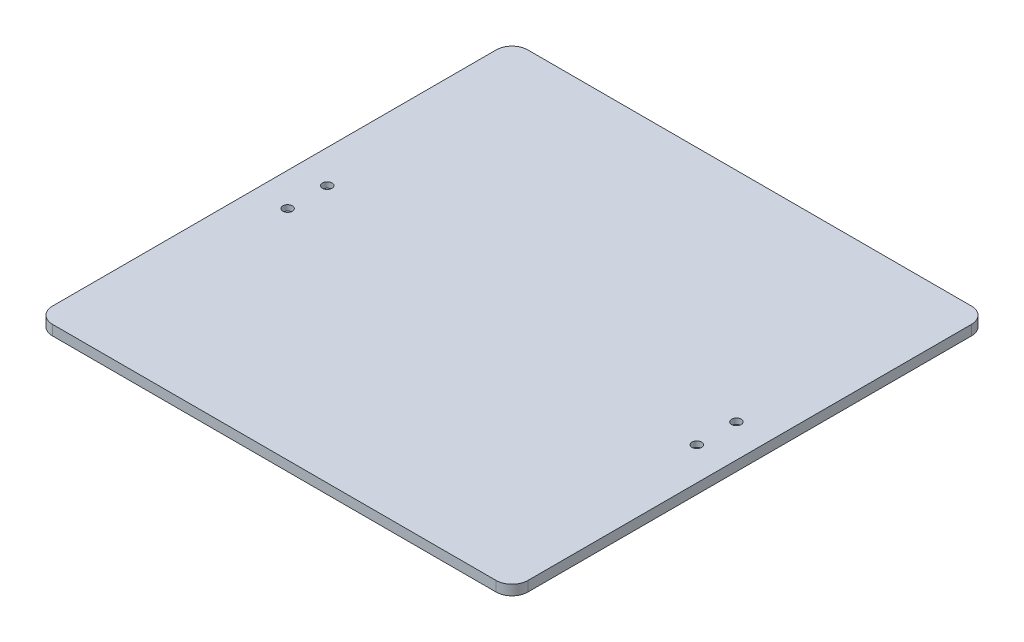
SolidWorks part; units mm, degrees
ref_plane "Front Plane" through (0, 0, 0) normal (0, 0, 1) x (1, 0, 0)
ref_plane "Top Plane" through (0, 0, 0) normal (0, 1, 0) x (1, 0, 0)
ref_plane "Right Plane" through (0, 0, 0) normal (1, 0, 0) x (0, 0, -1)
sketch "Sketch1" plane through (0, 0, 0) normal (0, 1, 0) x (1, 0, 0)
  line L1 (-150, 150) -> (150, 150)
  line L2 (-150, 150) -> (-150, -150)
  line L3 (-150, -150) -> (150, -150)
  line L4 (150, 150) -> (150, -150)
  line L5 (-150, 150) -> (150, -150) construction
  line L6 (-150, -150) -> (150, 150) construction
  point P0 (0, 0)
  dimension "D1" = 300
  dimension "D2" = 300
extrude "Boss-Extrude1" add sketch "Sketch1" along normal blind 6.35
fillet "Fillet1" radius 10 4 edges at (150, 3.175, -150) (150, 3.175, 150) (-150, 3.175, 150) (-150, 3.175, -150)
sketch "Sketch2" plane through (0, 6.35, 0) normal (0, 1, 0) x (1, 0, 0)
  line L0 (-150, 140) -> (-150, -140) construction
  line L1 (150, -140) -> (150, 140) construction
  line L2 (140, 150) -> (-140, 150) construction
  circle A0 centre (-129.12, 12.5) radius 1.75
  circle A1 centre (-129.12, -12.5) radius 1.75
  circle A2 centre (129.12, 12.5) radius 1.75
  circle A3 centre (129.12, -12.5) radius 1.75
  dimension "D1" = 3.5
  dimension "D2" = 3.5
  dimension "D3" = 3.5
  dimension "D4" = 3.5
  dimension "D5" = 20.88
  dimension "D6" = 20.88
  dimension "D7" = 20.88
  dimension "D8" = 20.88
  dimension "D9" = 137.5
  dimension "D10" = 137.5
  dimension "D11" = 25
  dimension "D12" = 25
extrude "Cut-Extrude1" cut sketch "Sketch2" against normal through all
sketch "Sketch3" plane through (0, 6.35, 0) normal (0, 1, 0) x (1, 0, 0)
  circle A0 centre (-129.12, 12.5) radius 3
  dimension "D1" = 6
extrude "Cut-Extrude2" cut sketch "Sketch3" against normal blind 3.5
pattern_linear "LPattern1" count 2 spacing 25 along (0, 0, 1) count 2 spacing 258.24 along (1, 0, 0) of "Cut-Extrude2"
